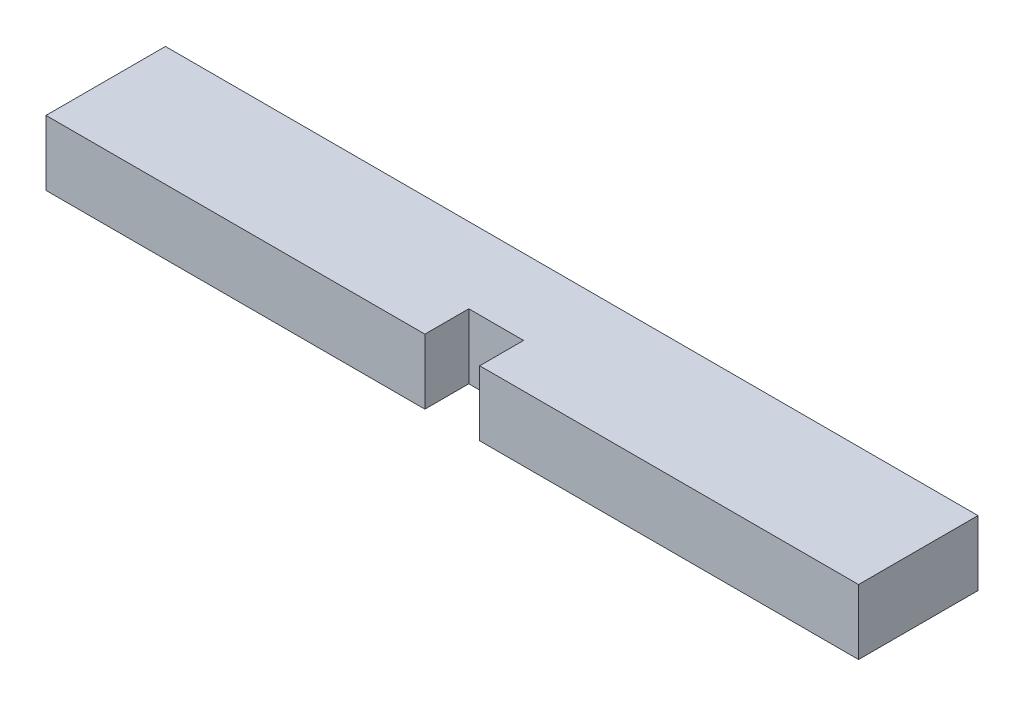
SolidWorks part; units mm, degrees
ref_plane "Front Plane" through (0, 0, 0) normal (0, 0, 1) x (1, 0, 0)
ref_plane "Top Plane" through (0, 0, 0) normal (0, 1, 0) x (1, 0, 0)
ref_plane "Right Plane" through (0, 0, 0) normal (1, 0, 0) x (0, 0, -1)
sketch "Sketch2" plane through (0, 0, 0) normal (0, 1, 0) x (1, 0, 0)
  line L1 (-30.2574, 4.0031) -> (28.4928, 4.0031)
  line L2 (-30.2574, 4.0031) -> (-30.2574, -4.6329)
  line L3 (-30.2574, -4.6329) -> (28.4928, -4.6329)
  line L4 (28.4928, 4.0031) -> (28.4928, -4.6329)
  dimension "D1" = 58.7502
  dimension "D2" = 8.636
extrude "Boss-Extrude1" add sketch "Sketch2" along normal blind 4.699
sketch "Sketch5" plane through (0, 0, 4.6329) normal (0, 0, 1) x (1, 0, 0)
  line L0 (-0.8823, 0) -> (-2.8635, 0)
  line L1 (-30.2574, 0) -> (28.4928, 0) construction
  line L2 (-2.8635, 0) -> (-2.8635, 4.699)
  line L3 (-30.2574, 4.699) -> (28.4928, 4.699) construction
  line L4 (-2.8635, 4.699) -> (1.0989, 4.699)
  line L5 (1.0989, 4.699) -> (1.0989, 0)
  line L6 (1.0989, 0) -> (-0.8823, 0)
  dimension "D1" = 1.9812
  dimension "D2" = 3.9624
extrude "Cut-Extrude1" cut sketch "Sketch5" against normal blind 3.175 and the other way through all
